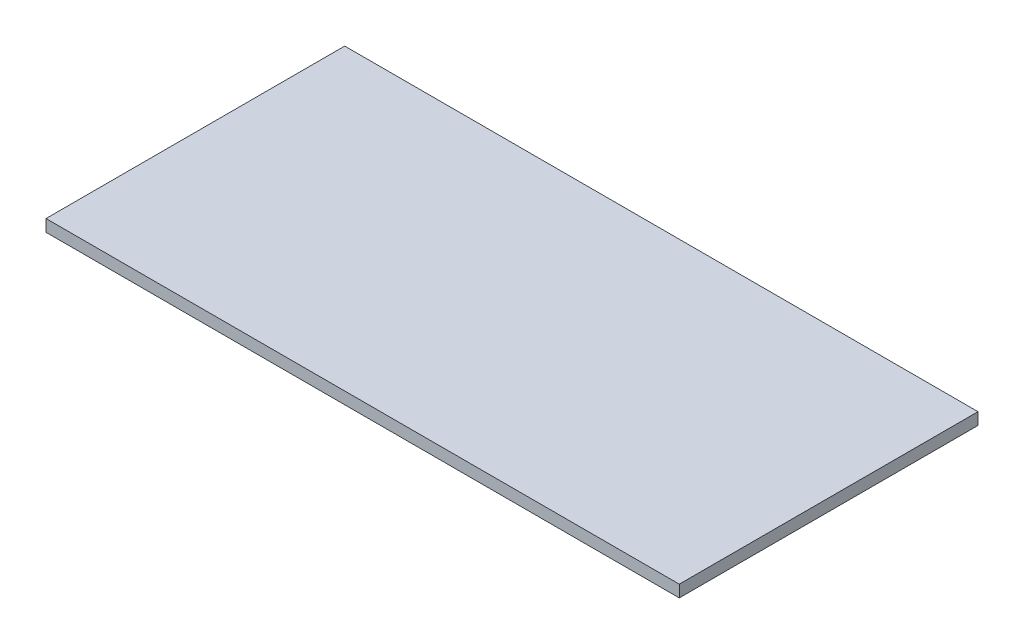
SolidWorks part; units mm, degrees
ref_plane "Plan de face" through (0, 0, 0) normal (0, 0, 1) x (1, 0, 0)
ref_plane "Plan de dessus" through (0, 0, 0) normal (0, 1, 0) x (1, 0, 0)
ref_plane "Plan de droite" through (0, 0, 0) normal (1, 0, 0) x (0, 0, -1)
sketch "Esquisse1" plane through (0, 0, 0) normal (0, 1, 0) x (1, 0, 0)
  line L1 (-26.5, 0) -> (26.5, 0)
  line L2 (-26.5, 0) -> (-26.5, -25)
  line L3 (-26.5, -25) -> (26.5, -25)
  line L4 (26.5, 0) -> (26.5, -25)
  point P4 (0, 0)
  dimension "D1" = 25
  dimension "D2" = 53
extrude "Boss.-Extru.1" add sketch "Esquisse1" along normal blind 1
